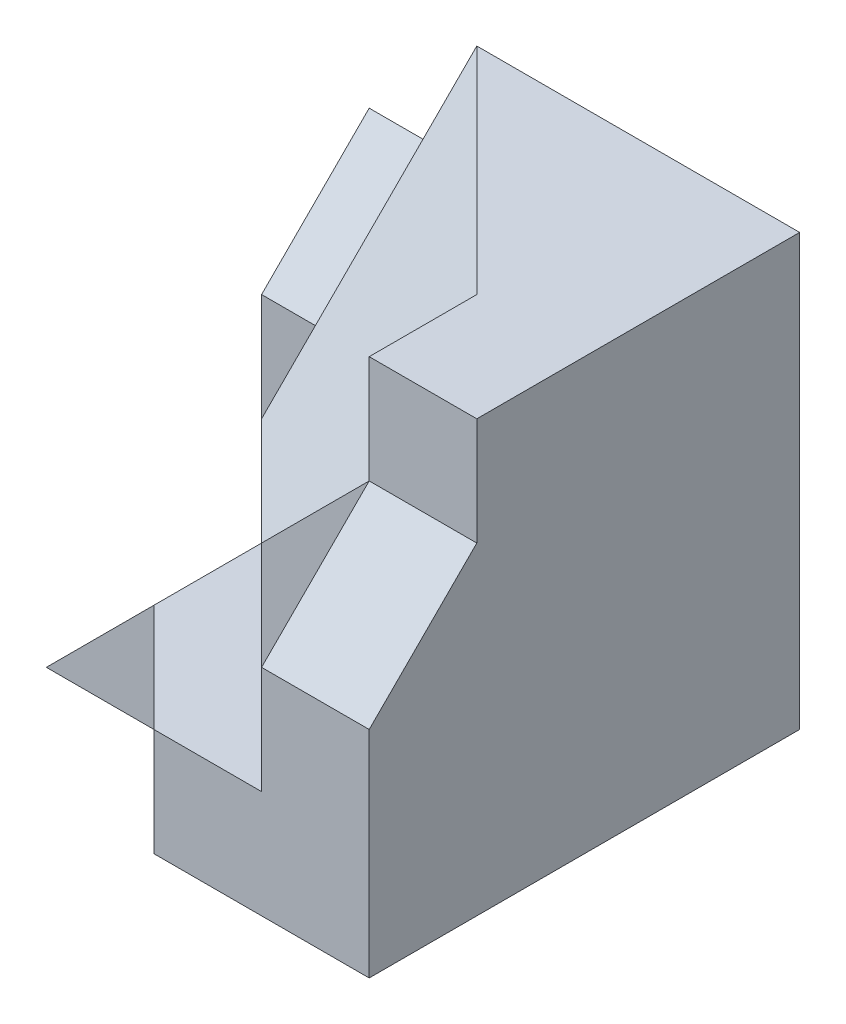
SolidWorks part; units mm, degrees
ref_plane "Front Plane" through (0, 0, 0) normal (0, 0, 1) x (1, 0, 0)
ref_plane "Top Plane" through (0, 0, 0) normal (0, 1, 0) x (1, 0, 0)
ref_plane "Right Plane" through (0, 0, 0) normal (1, 0, 0) x (0, 0, -1)
sketch "Sketch1" plane through (0, 0, 0) normal (0, 1, 0) x (1, 0, 0)
  line L0 (-15, 0) -> (0, 0)
  line L1 (0, 0) -> (0, -15)
  line L2 (0, -15) -> (-5, -15)
  line L3 (-5, -15) -> (-5, -10)
  line L4 (-5, -10) -> (-15, 0)
  dimension "D1" = 15
  dimension "D2" = 15
  dimension "D3" = 5
  dimension "D4" = 5
extrude "Boss-Extrude1" add sketch "Sketch1" along normal blind 20
sketch "Sketch2" plane through (0, 0, 15) normal (0, 0, 1) x (1, 0, 0)
  line L0 (-5, 15) -> (0, 15)
  line L1 (-5, 20) -> (-5, 0) construction
  line L2 (0, 20) -> (0, 0) construction
  line L3 (0, 15) -> (0, 0)
  line L4 (0, 0) -> (-5, 0)
  line L5 (-5, 0) -> (-5, 15)
  dimension "D1" = 15
extrude "Boss-Extrude3" add sketch "Sketch2" along normal blind 5
sketch "Sketch4" plane through (-5, 0, 0) normal (-1, 0, 0) x (0, 0, 1)
  line L0 (15, 15) -> (20, 10)
  line L1 (20, 15) -> (20, 0) construction
  line L2 (20, 10) -> (20, 15)
  line L3 (20, 15) -> (15, 15)
  dimension "D1" = 5
extrude "Cut-Extrude2" cut sketch "Sketch4" against normal blind 5
ref_plane "Plane1" through (0, 0, 0) normal (0, -1, 0) x (-1, 0, 0)
sketch "Sketch5" plane through (0, 0, 0) normal (0, -1, 0) x (-1, 0, 0)
  line L0 (15, 0) -> (15, -10)
  line L1 (15, -10) -> (10, -15)
  line L2 (10, -15) -> (5, -15)
  line L3 (5, -10) -> (5, -20) construction
  line L4 (5, -15) -> (5, -10)
  line L5 (5, -10) -> (15, 0)
  line L6 (15, 0) -> (5, -10) construction
  dimension "D1" = 5
  dimension "D2" = 5
extrude "Boss-Extrude4" add sketch "Sketch5" against normal blind 20
sketch3d "3DSketch1"
  line L0 (0, 20, 15) -> (0, 20, 0) construction
  line L1 (-10, 20, 15) -> (0, 20, 15) construction
  line L4 (-15, 20, 10) -> (-15, 20, 0) construction
  line L6 (-15, 20, 0) -> (-5, 20, 10)
  line L7 (-5, 20, 10) -> (-5, 15, 15)
  line L8 (-5, 15, 15) -> (-10, 10, 15)
  line L9 (-10, 10, 15) -> (-15, 10, 10)
  line L10 (-15, 10, 10) -> (-15, 20, 0)
  line L11 (-15, 20, 0) -> (-15, 0, 0) construction
  line L14 (-10, 20, 15) -> (-10, 0, 15) construction
  point P0 (-15, 20, 0)
  point P1 (-5, 20, 10)
  point P3 (-5, 15, 15)
  point P4 (-15, 10, 10)
  point P6 (-10, 10, 15)
  dimension "D1" = 5
  dimension "D2" = 5
  dimension "D3" = 10
  dimension "D4" = 10
  dimension "D5" = 10
extrude "Cut-Extrude3" cut sketch "3DSketch1" along direction (0, 0, -1) on the side against the normal blind 37
sketch "Sketch6" plane through (-15, 0, 0) normal (-1, 0, 0) x (0, 0, 1)
  line L0 (0, 0) -> (0, 15)
  line L1 (0, 20) -> (0, 0) construction
  line L2 (0, 15) -> (5, 10)
  line L3 (5, 10) -> (5, 0)
  line L4 (10, 0) -> (0, 0) construction
  line L5 (5, 0) -> (0, 0)
  dimension "D1" = 5
  dimension "D2" = 10
  dimension "D3" = 15
extrude "Boss-Extrude5" add sketch "Sketch6" along normal blind 5
sketch "Sketch7" plane through (0, 0, 5) normal (0, 0, 1) x (1, 0, 0)
  line L0 (-15, 0) -> (-15, 10) construction
  line L1 (-20, 0) -> (-15, 0)
  line L2 (-20, 0) -> (-20, 5)
  line L3 (-20, 5) -> (-15, 5)
  line L4 (-15, 0) -> (-15, 5)
  dimension "D1" = 5
extrude "Boss-Extrude6" add sketch "Sketch7" along normal blind 10
sketch "Sketch8" plane through (0, 0, 15) normal (0, 0, 1) x (1, 0, 0)
  line L0 (-20, 0) -> (-15, 5)
  line L1 (-15, 5) -> (-20, 5)
  line L2 (-20, 5) -> (-20, 0)
extrude "Cut-Extrude4" cut sketch "Sketch8" against normal blind 10
sketch "Sketch9" plane through (0, 0, 0) normal (0, -1, 0) x (-1, 0, 0)
  line L0 (15, -15) -> (15, -10)
  line L1 (15, -10) -> (10, -15)
  line L2 (10, -15) -> (5, -15)
  line L3 (5, -15) -> (5, -20)
  line L4 (5, -20) -> (10, -20)
  line L5 (10, -20) -> (15, -15)
extrude "Boss-Extrude7" add sketch "Sketch9" against normal blind 5
